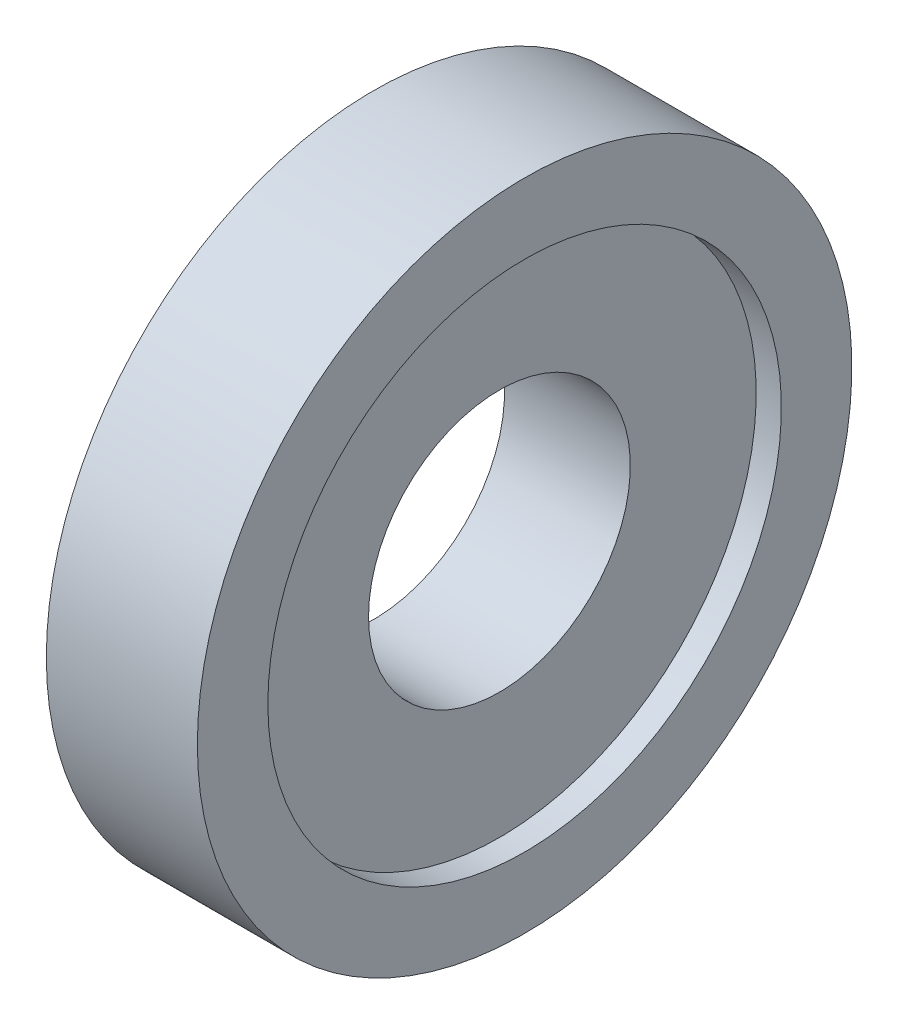
SolidWorks part; units mm, degrees
material "POM 乙缩醛共聚物"
ref_plane "前视基准面" through (0, 0, 0) normal (0, 0, 1) x (1, 0, 0)
ref_plane "上视基准面" through (0, 0, 0) normal (0, 1, 0) x (1, 0, 0)
ref_plane "右视基准面" through (0, 0, 0) normal (1, 0, 0) x (0, 0, -1)
sketch "草图1" plane through (0, 0, 0) normal (0, 0, 1) x (1, 0, 0)
  line L0 (0, 0) -> (4.0926, 0) construction
  line L1 (0, 0) -> (0, 2.6) construction
  line L2 (0, 2.6) -> (0, 6.5)
  line L3 (0, 6.5) -> (3, 6.5)
  line L4 (3, 6.5) -> (3, 5.1)
  line L5 (3, 5.1) -> (2.5, 5.1)
  line L6 (2.5, 5.1) -> (2.5, 2.6)
  line L7 (2.5, 2.6) -> (0, 2.6)
  dimension "D1" = 13
  dimension "D2" = 5.2
  dimension "D3" = 10.2
  dimension "D4" = 3
  dimension "D5" = 0.5
revolve "旋转1" add sketch "草图1" angle 360 about L0
